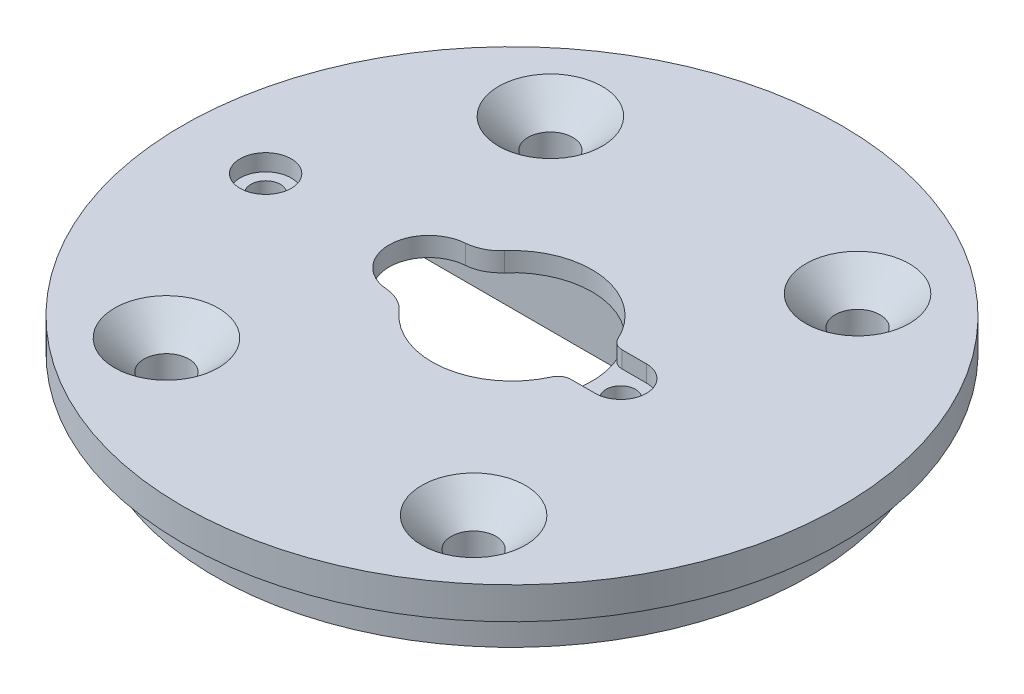
SolidWorks part; units mm, degrees
ref_plane "Спереди" through (0, 0, 0) normal (0, 0, 1) x (1, 0, 0)
ref_plane "Сверху" through (0, 0, 0) normal (0, 1, 0) x (1, 0, 0)
ref_plane "Справа" through (0, 0, 0) normal (1, 0, 0) x (0, 0, -1)
sketch "Эскиз1" plane through (0, 0, 0) normal (0, 1, 0) x (1, 0, 0)
  line L0 (29, 26) -> (29, 0) construction
  line L1 (0, 0) -> (58, 0)
  line L2 (0, 0) -> (0, 26) construction
  line L3 (0, 26) -> (58, 26)
  line L4 (58, 0) -> (58, 26) construction
  line L5 (-1.068, 24) -> (59.068, 24)
  line L6 (-1.9215, 22) -> (59.9215, 22)
  line L7 (0, 13) -> (58, 13) construction
  line L8 (-1.068, 2) -> (59.068, 2)
  line L9 (-1.9215, 4) -> (59.9215, 4)
  arc A0 (0, 26) -> (0, 0) centre (21.9374, 13) ccw
  arc A1 (58, 26) -> (58, 0) centre (36.0626, 13) cw
  circle A2 centre (29, 13) radius 25.75
  dimension "D2" = 25.5
  dimension "D6" = 51.5
  dimension "D1" = 58
  dimension "D3" = 26
  dimension "D4" = 2
  dimension "D5" = 2
extrude "Бобышка-Вытянуть1" add sketch "Эскиз1" along normal blind 6 contours A2 L6 A0 L9 | L9 A2 L6 | A2 L9 A1 L6 | A2 L5 A0 L6 | A2 L3 A0 L5 | L6 A2 L5 | L5 A2 L3 | L3 A2 | A2 L5 A1 L3 | A2 L6 A1 L5 | A2 L9 A0 L8 | A2 L8 A0 L1 | L8 A2 L9 | L1 A2 L8 | L1 A2 | A2 L8 A1 L9 | A2 L1 A1 L8
sketch "Эскиз2" plane through (0, 6, 0) normal (0, -1, 0) x (1, 0, 0)
  circle A0 centre (29, -13) radius 6.25
  circle A1 centre (22.5, -13) radius 3.1
  circle A2 centre (37.5, -13) radius 1.15
  circle A3 centre (9.75, -13) radius 1.15
  dimension "D1" = 12.5
  dimension "D2" = 6.2
  dimension "D4" = 27.75
  dimension "D5" = 2.3
  dimension "D3" = 6.5
  dimension "D6" = 8.5
extrude "Вырез-Вытянуть1" cut sketch "Эскиз2" along normal through all contours A0 A1 | A1 A0 | A1 A0 | A3 | A2
fillet "Скругление1" radius 3 2 edges at (23.4844, 3, -15.9395) (23.4844, 3, -10.0605)
sketch "Эскиз7" plane through (0, 0, 0) normal (0, -1, 0) x (1, 0, 0)
  line L1 (11.5, -6.5) -> (35.5, -6.5)
  line L2 (11.5, -6.5) -> (11.5, -19.5)
  line L3 (11.5, -19.5) -> (35.5, -19.5)
  line L4 (35.5, -6.5) -> (35.5, -19.5)
  circle A0 centre (29, -13) radius 6.5
  dimension "D1" = 24
  dimension "D2" = 13
extrude "Вырез-Вытянуть4" cut sketch "Эскиз7" against normal blind 4.5
fillet "Скругление4" radius 2 4 edges at (0, 3, 0) (0, 3, -26) (58, 3, 0) (58, 3, -26)
sketch "Эскиз12" plane through (0, 0, 0) normal (0, -1, 0) x (1, 0, 0)
  circle A0 centre (29, -13) radius 23.25
  circle A1 centre (29, -13) radius 25.75
  circle A2 centre (29, -13) radius 32.5626
  arc A3 (-0.5965, -1.0638) -> (-0.5965, -24.9362) centre (21.9374, -13) ccw construction
  line M9 (6.7725, 0) -> (1.1709, 0)
  line M13 (1.1709, -26) -> (6.7725, -26)
  line M15 (51.2275, -26) -> (56.8291, -26)
  line M19 (56.8291, 0) -> (51.2275, 0)
  dimension "D1" = 46.5
  dimension "D2" = 2.5
extrude "Вырез-Вытянуть9" cut sketch "Эскиз12" against normal blind 3.5 contours A1 A0 M9 M13 | A1 A0 M15 M19
sketch "Эскиз13" plane through (0, 0, 0) normal (0, -1, 0) x (1, 0, 0)
  circle A0 centre (29, -13) radius 25.75
  circle A1 centre (29, -13) radius 32.5626
  arc A2 (6.7725, 0) -> (6.7725, -26) centre (29, -13) ccw construction
  arc A3 (58.5965, -1.0638) -> (58.5965, -24.9362) centre (36.0626, -13) ccw construction
extrude "Вырез-Вытянуть10" cut sketch "Эскиз13" against normal through all
sketch "Эскиз9" plane through (0, 6, 0) normal (0, 1, 0) x (1, 0, 0)
  circle A0 centre (29, 13) radius 17.625
  circle A1 centre (29, 13) radius 15.125
  dimension "D1" = 2.5
  dimension "D2" = 35.25
extrude "Вырез-Вытянуть5" [suppressed] cut sketch "Эскиз9" against normal blind 2
fillet "Скругление6" [suppressed] radius 1
fillet "Скругление7" [suppressed] radius 2
sketch "Эскиз10" plane through (0, 0, 0) normal (0, -1, 0) x (1, 0, 0)
  circle A4 centre (29, -13) radius 17 construction
  circle A5 centre (46, -13) radius 1.6
  circle A6 centre (20.5, -27.7224) radius 1.6
  circle A7 centre (20.5, 1.7224) radius 1.6
  point P13 (29, -13)
  dimension "D1" = 3.2
  dimension "D2" = 34
  dimension "D3" = 3
extrude "Вырез-Вытянуть6" [suppressed] cut sketch "Эскиз10" against normal through all
sketch "Эскиз11" [suppressed] plane through (0, 6, 0) normal (0, 1, 0) x (1, 0, 0)
  line L1 (23.7332, 27.7224) -> (22.1166, 30.5224)
  line L2 (22.1166, 30.5224) -> (18.8834, 30.5224)
  line L3 (18.8834, 30.5224) -> (17.2668, 27.7224)
  line L4 (17.2668, 27.7224) -> (18.8834, 24.9224)
  line L5 (18.8834, 24.9224) -> (22.1166, 24.9224)
  line L6 (22.1166, 24.9224) -> (23.7332, 27.7224)
  line L25 (49.2332, 13) -> (47.6166, 15.8)
  line L26 (47.6166, 15.8) -> (44.3834, 15.8)
  line L27 (44.3834, 15.8) -> (42.7668, 13)
  line L28 (42.7668, 13) -> (44.3834, 10.2)
  line L29 (44.3834, 10.2) -> (47.6166, 10.2)
  line L30 (47.6166, 10.2) -> (49.2332, 13)
  line L31 (23.7332, -1.7224) -> (22.1166, 1.0776)
  line L32 (22.1166, 1.0776) -> (18.8834, 1.0776)
  line L33 (18.8834, 1.0776) -> (17.2668, -1.7224)
  line L34 (17.2668, -1.7224) -> (18.8834, -4.5224)
  line L35 (18.8834, -4.5224) -> (22.1166, -4.5224)
  line L36 (22.1166, -4.5224) -> (23.7332, -1.7224)
  circle A0 centre (20.5, 27.7224) radius 2.8 construction
  circle A1 centre (46, 13) radius 2.8 construction
  circle A2 centre (20.5, -1.7224) radius 2.8 construction
  dimension "D1" = 5.6
extrude "Вырез-Вытянуть7" [suppressed] cut sketch "Эскиз11" against normal blind 4
sketch "Эскиз14" plane through (0, 0, 0) normal (0, -1, 0) x (1, 0, 0)
  line L0 (35.5, -6.5) -> (35.5, -19.5) construction
  line L1 (35.5, -6.5) -> (40.5, -6.5)
  line L2 (35.5, -6.5) -> (35.5, -19.5)
  line L3 (35.5, -19.5) -> (40.5, -19.5)
  line L4 (40.5, -6.5) -> (40.5, -19.5)
  line L5 (23.5, -6.5) -> (23.5, -19.5) construction
  line L6 (11.5, -6.5) -> (35.5, -6.5) construction
  line L7 (11.5, -19.5) -> (35.5, -19.5) construction
  line L13 (11.5, -6.5) -> (5.75, -6.5)
  line L14 (11.5, -6.5) -> (11.5, -19.5)
  line L15 (11.5, -19.5) -> (5.75, -19.5)
  line L16 (5.75, -6.5) -> (5.75, -19.5)
  circle A0 centre (29, -13) radius 23.25 construction
  dimension "D1" = 5
extrude "Вырез-Вытянуть11" cut sketch "Эскиз14" against normal blind 0.5
sketch "Эскиз15" plane through (0, 6, 0) normal (0, 1, 0) x (1, 0, 0)
  line L0 (37.5, 11) -> (34.9214, 11)
  line L1 (37.5, 15) -> (34.9214, 15)
  circle A0 centre (37.5, 13) radius 2
  circle A1 centre (9.75, 13) radius 2
  arc A2 (24.2909, 8.8906) -> (24.2909, 17.1094) centre (29, 13) ccw construction
  circle M20 centre (37.5, 13) radius 1.15
  circle M21 centre (9.75, 13) radius 1.15
  arc M22 (24.2909, 17.1094) -> (24.2909, 8.8906) centre (29, 13) cw
  dimension "D1" = 4
extrude "Вырез-Вытянуть12" cut sketch "Эскиз15" against normal blind 1.3 contours A0 M20 | A0 L1 L0 M22 | A1 M21
sketch "Эскиз16" plane through (0, 0, 0) normal (0, -1, 0) x (1, 0, 0)
  line L1 (17, -28) -> (41, -28) construction
  line L2 (17, -28) -> (17, 2) construction
  line L3 (17, 2) -> (41, 2) construction
  line L4 (41, -28) -> (41, 2) construction
  line L5 (17, -28) -> (41, 2) construction
  line L6 (17, 2) -> (41, -28) construction
  circle A0 centre (41, 2) radius 1.75
  circle A1 centre (41, -28) radius 1.75
  circle A2 centre (17, -28) radius 1.75
  circle A3 centre (17, 2) radius 1.75
  point P0 (29, -13)
  dimension "D3" = 3.5
  dimension "D1" = 24
  dimension "D2" = 30
extrude "Вырез-Вытянуть13" cut sketch "Эскиз16" against normal through all
fillet "Скругление8" radius 1 2 edges at (34.9214, 5.35, -11) (34.9214, 5.35, -15)
chamfer "Фаска1" distance 2.3 angle 45 4 edges at (41, 6, 0.25) (41, 6, -29.75) (17, 6, -29.75) (17, 6, 0.25)
